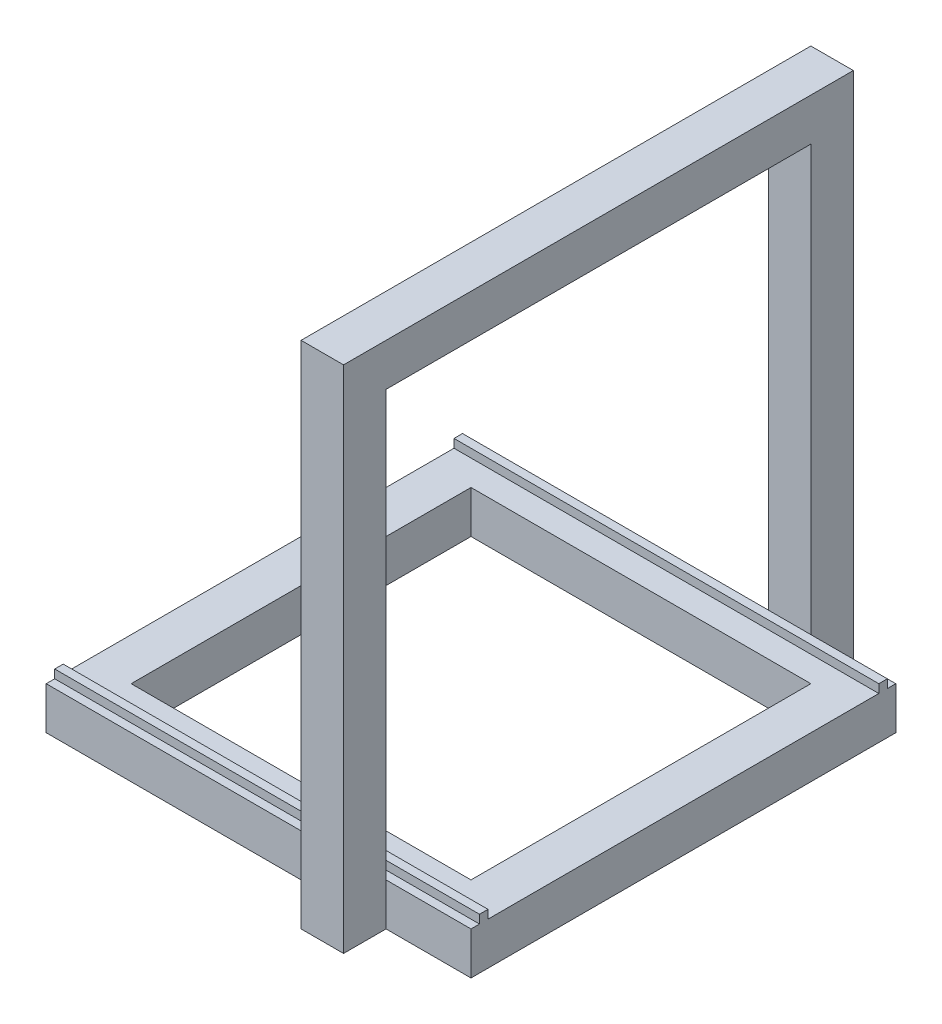
SolidWorks part; units mm, degrees
ref_plane "Front Plane" through (0, 0, 0) normal (0, 0, 1) x (1, 0, 0)
ref_plane "Top Plane" through (0, 0, 0) normal (0, 1, 0) x (1, 0, 0)
ref_plane "Right Plane" through (0, 0, 0) normal (1, 0, 0) x (0, 0, -1)
sketch "Sketch2" plane through (0, 0, 0) normal (0, 1, 0) x (1, 0, 0)
  line L1 (-250, -250) -> (250, -250)
  line L2 (-250, -250) -> (-250, 250)
  line L3 (-250, 250) -> (250, 250)
  line L4 (250, -250) -> (250, 250)
  line L5 (-250, -250) -> (250, 250) construction
  line L6 (-250, 250) -> (250, -250) construction
  point P0 (0, 0)
  dimension "D1" = 500
  dimension "D2" = 500
extrude "Boss-Extrude1" add sketch "Sketch2" along normal blind 50 contours L2 L3 L4 L1
sketch "Sketch7" plane through (0, 50, 0) normal (0, 1, 0) x (1, 0, 0)
  line L1 (200, 200) -> (-200, 200)
  line L2 (200, 200) -> (200, -200)
  line L3 (200, -200) -> (-200, -200)
  line L4 (-200, 200) -> (-200, -200)
  line L5 (200, 200) -> (-200, -200) construction
  line L6 (200, -200) -> (-200, 200) construction
  point P0 (0, 0)
  dimension "D1" = 400
  dimension "D2" = 400
extrude "Cut-Extrude1" cut sketch "Sketch7" against normal blind 550
sketch "Sketch8" plane through (0, 50, 0) normal (0, 1, 0) x (1, 0, 0)
  line L0 (-250, -250) -> (-250, 250) construction
  line L1 (-250, 240) -> (250, 240)
  line L2 (-250, 240) -> (-250, 230)
  line L3 (-250, 230) -> (250, 230)
  line L4 (250, 240) -> (250, 230)
  line L5 (250, -250) -> (250, 250) construction
  line L6 (-250, 250) -> (250, 250) construction
  line L7 (-250, -230) -> (250, -230)
  line L8 (-250, -230) -> (-250, -240)
  line L9 (-250, -240) -> (250, -240)
  line L10 (250, -230) -> (250, -240)
  line L11 (-250, -250) -> (250, -250) construction
  dimension "D1" = 10
  dimension "D2" = 10
  dimension "D3" = 10
  dimension "D4" = 10
extrude "Boss-Extrude2" add sketch "Sketch8" along normal blind 10
sketch "Sketch9" plane through (0, 0, 0) normal (0, -1, 0) x (1, 0, 0)
  line L0 (-250, -250) -> (250, -250) construction
  line L1 (100, -250) -> (150, -250)
  line L2 (100, -250) -> (100, -300)
  line L3 (100, -300) -> (150, -300)
  line L4 (150, -250) -> (150, -300)
  line L5 (-250, 250) -> (250, 250) construction
  line L6 (100, 250) -> (150, 250)
  line L7 (100, 250) -> (100, 300)
  line L8 (100, 300) -> (150, 300)
  line L9 (150, 250) -> (150, 300)
  line L10 (250, 250) -> (250, -250) construction
  dimension "D1" = 50
  dimension "D2" = 100
  dimension "D3" = 50
extrude "Boss-Extrude3" add sketch "Sketch9" against normal blind 550
sketch "Sketch10" plane through (0, 0, 300) normal (0, 0, 1) x (1, 0, 0)
  line L0 (150, 550) -> (150, 0) construction
  line L1 (100, 550) -> (150, 550)
  line L2 (100, 550) -> (100, 600)
  line L3 (100, 600) -> (150, 600)
  line L4 (150, 550) -> (150, 600)
  dimension "D1" = 50
extrude "Boss-Extrude4" add sketch "Sketch10" against normal blind 600
